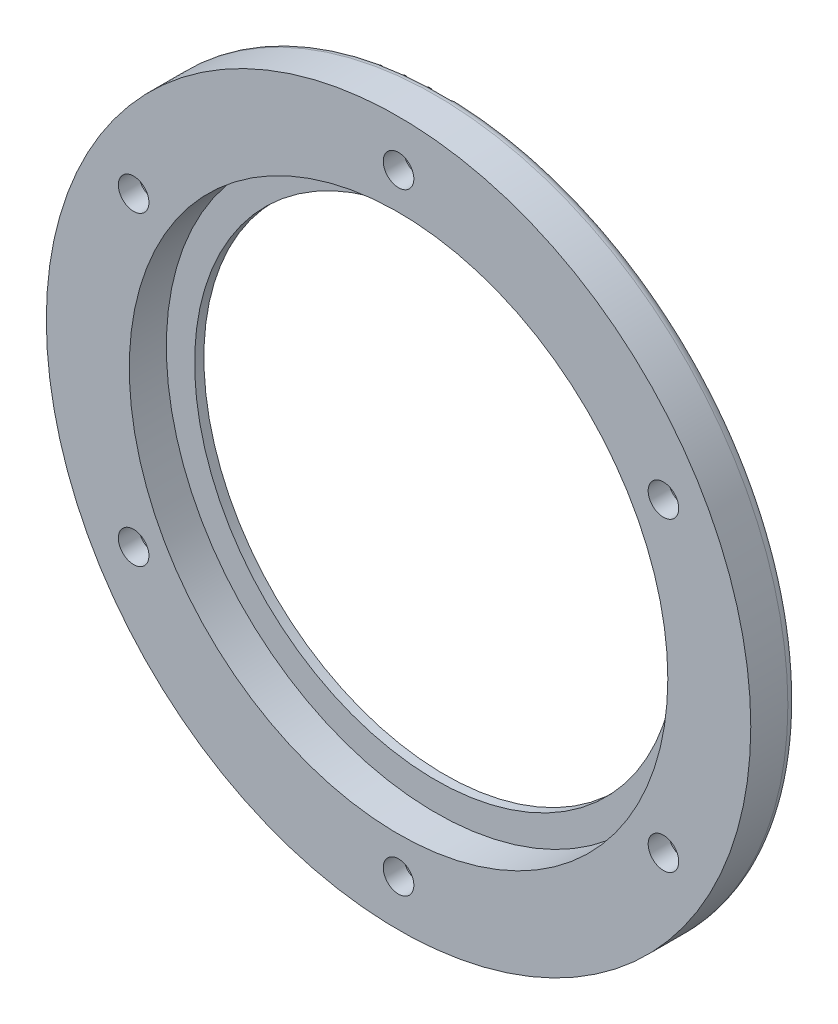
SolidWorks part; units mm, degrees
ref_plane "前视基准面" through (0, 0, 0) normal (0, 0, 1) x (1, 0, 0)
ref_plane "上视基准面" through (0, 0, 0) normal (0, 1, 0) x (1, 0, 0)
ref_plane "右视基准面" through (0, 0, 0) normal (1, 0, 0) x (0, 0, -1)
sketch "草图1" plane through (0, 0, 0) normal (0, 1, 0) x (1, 0, 0)
  line L0 (38, 29) -> (0, 29)
  line L1 (0, 29) -> (0, 24)
  line L2 (0, 24) -> (38, 24)
  line L3 (38, 24) -> (38, 29)
  line L4 (0, 29) -> (0, 24) construction
revolve "旋转1" add sketch "草图1" angle 360 about L4
hole_wizard "M48 六角头螺栓的柱形沉头孔1" positions "草图15" profile "草图14" counterbore size "M48" standard "ANSI Metric"
sketch "草图15" plane through (0, 0, -24) normal (0, 0, 1) x (1, 0, 0)
  point P0 (0, 0)
sketch "草图14" plane through (0, 0, -24) normal (1, 0, 0) x (0, -1, 0)
  line L0 (0, 0) -> (0, 5)
  line L1 (0, 5) -> (26, 5)
  line L3 (26, 5) -> (26, 4)
  line L4 (26, 4) -> (29.05, 4)
  line L5 (29.05, 4) -> (29.05, 0)
  line L7 (29.05, 0) -> (0, 0)
  line L11 (0, -6.35) -> (0, 107.95) construction
  dimension "通孔孔直径" = 52
  dimension "通孔孔深度" = 5
  dimension "柱形沉头孔直径" = 58.1
  dimension "柱形沉头孔深度" = 4
sketch "草图16" plane through (0, 0, -29) normal (0, 0, -1) x (-1, 0, 0)
  circle A0 centre (0, -33) radius 1.65
  circle A1 centre (-28.5788, -16.5) radius 1.65
  circle A2 centre (-28.5788, 16.5) radius 1.65
  circle A3 centre (0, 33) radius 1.65
  circle A4 centre (28.5788, 16.5) radius 1.65
  circle A5 centre (28.5788, -16.5) radius 1.65
  point P16 (0, 0)
  dimension "D2" = 3.3
  dimension "D1" = 33
  dimension "D3" = 6
extrude "切除-拉伸9" cut sketch "草图16" against normal through all
sketch "草图17" plane through (0, 0, -29) normal (0, 0, -1) x (-1, 0, 0)
  line L0 (0, 0) -> (-28.5788, 16.5) construction
  circle A0 centre (0, -33) radius 3
  circle A1 centre (-28.5788, -16.5) radius 3
  circle A2 centre (-28.5788, 16.5) radius 3
  circle A3 centre (0, 33) radius 3
  circle A4 centre (28.5788, 16.5) radius 3
  circle A5 centre (28.5788, -16.5) radius 3
  point P16 (0, 0)
  dimension "D1" = 6
extrude "切除-拉伸10" cut sketch "草图17" against normal blind 2.8
fillet "圆角2" radius 1 1 edges at (38, 0, -29)
